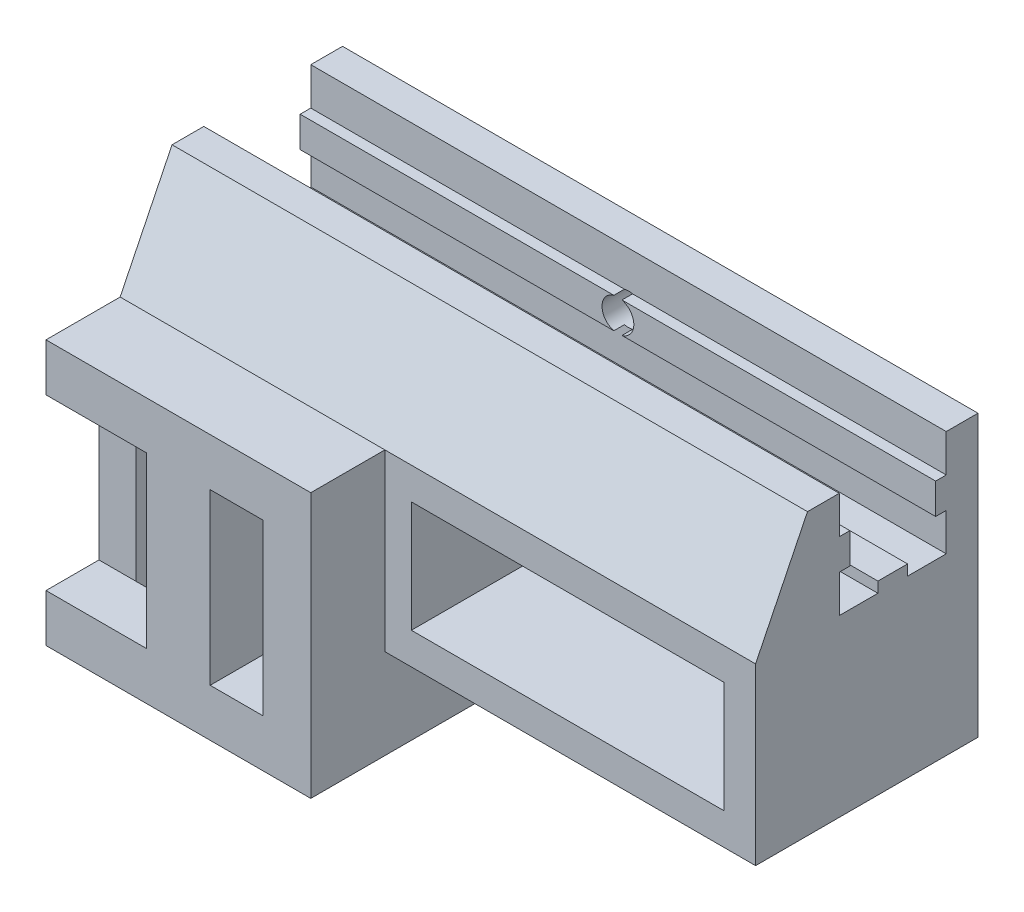
SolidWorks part; units mm, degrees
ref_plane "Front Plane" through (0, 0, 0) normal (0, 0, 1) x (1, 0, 0)
ref_plane "Top Plane" through (0, 0, 0) normal (0, 1, 0) x (1, 0, 0)
ref_plane "Right Plane" through (0, 0, 0) normal (1, 0, 0) x (0, 0, -1)
sketch "Esquisse1" plane through (0, 0, 0) normal (0, 0, 1) x (1, 0, 0)
  line L1 (-30, 17.5) -> (30, 17.5)
  line L2 (-30, 17.5) -> (-30, -17.5)
  line L3 (-30, -17.5) -> (30, -17.5)
  line L4 (30, 17.5) -> (30, -17.5)
  point P4 (-30, 0)
  point P6 (0, 17.5)
  dimension "D1" = 35
  dimension "D2" = 60
extrude "Main" add sketch "Esquisse1" along normal blind 3
sketch "Esquisse2" plane through (0, 0, 3) normal (0, 0, 1) x (1, 0, 0)
  line L0 (-30, 17.5) -> (-30, -17.5) construction
  line L1 (-30, 11.05) -> (30, 11.05)
  line L2 (-30, 11.05) -> (-30, 13.95)
  line L3 (-30, 13.95) -> (30, 13.95)
  line L4 (30, 11.05) -> (30, 13.95)
  line L5 (30, -17.5) -> (30, 17.5) construction
  line L6 (30, 17.5) -> (-30, 17.5) construction
  point P8 (-30, 12.5)
  dimension "D1" = 5
  dimension "D2" = 2.9
extrude "HorizontalMakerBeamRail1" add sketch "Esquisse2" along normal blind 1
sketch "Esquisse3" plane through (0, 0, 0) normal (0, 0, -1) x (-1, 0, 0)
  line L0 (-30, 11.05) -> (-30, 13.95) construction
  line L1 (-30, 17.5) -> (30, 17.5) construction
  circle A0 centre (0, 12.5) radius 1.5
  point P6 (-30, 12.5)
  point P9 (0, 17.5)
  dimension "D1" = 3
extrude "VerticalFixHole" cut sketch "Esquisse3" against normal through all
sketch "Esquisse4" plane through (0, 0, 3) normal (0, 0, 1) x (1, 0, 0)
  line L0 (-30, -17.5) -> (30, -17.5) construction
  line L1 (-30, -17.5) -> (-5, -17.5)
  line L2 (-30, -17.5) -> (-30, 7.5)
  line L3 (-30, 7.5) -> (-5, 7.5)
  line L4 (-5, -17.5) -> (-5, 7.5)
  line L5 (-30, 11.05) -> (-30, -17.5) construction
  line L6 (30, 17.5) -> (-30, 17.5) construction
  line L7 (-26.5, 4) -> (-8.5, 4)
  line L8 (-26.5, 4) -> (-26.5, -14)
  line L9 (-26.5, -14) -> (-8.5, -14)
  line L10 (-8.5, 4) -> (-8.5, -14)
  point P6 (-17.5, 4)
  point P13 (-17.5, 7.5)
  point P14 (-26.5, -5)
  point P15 (-30, -5)
  dimension "D1" = 10
  dimension "D2" = 18
  dimension "D3" = 3.5
extrude "UrgencyButton" add sketch "Esquisse4" along normal blind 20
sketch "Esquisse5" plane through (0, 0, 23) normal (0, 0, 1) x (1, 0, 0)
  line L1 (-26.5, 4) -> (-8.5, 4)
  line L2 (-26.5, 4) -> (-26.5, -14)
  line L3 (-26.5, -14) -> (-8.5, -14)
  line L4 (-8.5, 4) -> (-8.5, -14)
extrude "UrgencyButtonHole" cut sketch "Esquisse5" against normal through all and the other way through all
sketch "Esquisse6" plane through (0, 0, 23) normal (0, 0, 1) x (1, 0, 0)
  line L0 (-5, 7.5) -> (-30, 7.5) construction
  line L1 (-30, -17.5) -> (-5, -17.5)
  line L2 (-5, -17.5) -> (-5, 7.5)
  line L4 (-30, 7.5) -> (-30, 3)
  line L5 (-30, -17.5) -> (-5, -17.5) construction
  line L6 (-8.5, 4) -> (-26.5, 4) construction
  line L7 (-9.5, 3) -> (-30, 3)
  line L8 (-9.5, 3) -> (-9.5, -13)
  line L9 (-9.5, -13) -> (-30, -13)
  line L12 (-8.5, -14) -> (-8.5, 4) construction
  line L13 (-30, -13) -> (-30, -17.5)
  line L15 (-5, 7.5) -> (-30, 7.5)
  line L16 (-30, 7.5) -> (-30, -17.5) construction
  dimension "D2" = 1
  dimension "D3" = 1
extrude "Boss.-Extru.4" add sketch "Esquisse6" along normal blind 5
sketch "Esquisse7" plane through (0, 0, 28) normal (0, 0, 1) x (1, 0, 0)
  line L0 (-5, 7.5) -> (-30, 7.5) construction
  line L1 (-20.5, 7.5) -> (-14.5, 7.5)
  line L2 (-20.5, 7.5) -> (-20.5, -17.5)
  line L3 (-20.5, -17.5) -> (-14.5, -17.5)
  line L4 (-14.5, 7.5) -> (-14.5, -17.5)
  line L5 (-30, -17.5) -> (-5, -17.5) construction
  line L6 (-26.5, 3) -> (-26.5, -13) construction
  dimension "D1" = 6
  dimension "D2" = 6
extrude "Boss.-Extru.5" add sketch "Esquisse7" against normal up to surface (5 mm away) up to face at (-28.25, -5, 23)
sketch "Esquisse8" plane through (0, 0, 0) normal (0, 0, -1) x (-1, 0, 0)
  line L0 (5, -17.5) -> (5, 7.5) construction
  line L1 (2.5, -6) -> (-27, -6)
  line L2 (2.5, -6) -> (2.5, 4.5)
  line L3 (2.5, 4.5) -> (-27, 4.5)
  line L4 (-27, -6) -> (-27, 4.5)
  line L5 (-30, 17.5) -> (30, 17.5) construction
  dimension "D1" = 10.5
  dimension "D2" = 29.5
  dimension "D3" = 2.5
  dimension "D4" = 13
extrude "SwitchHole" cut sketch "Esquisse8" against normal through all
sketch "Esquisse10" plane through (0, 0, 3) normal (0, 0, 1) x (1, 0, 0)
  line L0 (-5, -17.5) -> (-5, 7.5) construction
  line L1 (-5, -9) -> (30, -9)
  line L2 (-5, -9) -> (-5, 7.5)
  line L3 (-5, 7.5) -> (30, 7.5)
  line L4 (30, -9) -> (30, 7.5)
  line L6 (-2.5, -6) -> (27, -6) construction
  line L7 (27, -6) -> (27, 4.5) construction
  line L8 (30, -17.5) -> (30, 11.05) construction
  line L9 (-2.5, -6) -> (27, -6)
  line L10 (-2.5, -6) -> (-2.5, 4.5)
  line L11 (-2.5, 4.5) -> (27, 4.5)
  line L12 (27, -6) -> (27, 4.5)
  line L13 (-5, 7.5) -> (-30, 7.5) construction
  dimension "D1" = 3
  dimension "D2" = 3
extrude "Boss.-Extru.6" add sketch "Esquisse10" along normal blind 18
sketch "Esquisse11" plane through (0, 0, 3) normal (0, 0, 1) x (1, 0, 0)
  line L1 (-5, -9) -> (30, -9)
  line L2 (-5, -9) -> (-5, -17.5)
  line L3 (-5, -17.5) -> (30, -17.5)
  line L4 (30, -9) -> (30, -17.5)
extrude "Enlèv. mat.-Extru.4" cut sketch "Esquisse11" against normal through all
sketch "Esquisse12" plane through (0, 7.5, 0) normal (0, 1, 0) x (1, 0, 0)
  line L0 (30, -21) -> (30, -3) construction
  line L1 (-30, -9.45) -> (30, -9.45)
  line L2 (-30, -9.45) -> (-30, -6.65)
  line L3 (-30, -6.65) -> (30, -6.65)
  line L4 (30, -9.45) -> (30, -6.65)
  line L5 (-30, -28) -> (-30, -3) construction
  point P9 (-30, -8.05)
  dimension "D1" = 2.8
  dimension "D2" = 5.05
extrude "Boss.-Extru.7" add sketch "Esquisse12" along normal blind 1
sketch "Esquisse13" plane through (30, 0, 0) normal (1, 0, 0) x (0, 0, -1)
  line L0 (-4, 13.95) -> (-3, 13.95) construction
  line L1 (-21, 7.5) -> (-9.45, 7.5) construction
  line L2 (-4, 11.05) -> (-3, 11.05) construction
  line L3 (-13.1, 7.5) -> (-13.1, 11.05)
  line L4 (-13.1, 11.05) -> (-12.1, 11.05)
  line L5 (-12.1, 11.05) -> (-12.1, 13.95)
  line L6 (-12.1, 13.95) -> (-13.1, 13.95)
  line L7 (-13.1, 13.95) -> (-13.1, 17.5)
  line L8 (-13.1, 17.5) -> (-16.1, 17.5)
  line L9 (-16.1, 17.5) -> (-16.1, 7.5)
  line L10 (-16.1, 7.5) -> (-13.1, 7.5)
  line L12 (-3, 7.5) -> (-3, 11.05) construction
  line L13 (-3, 17.5) -> (0, 17.5) construction
  point P5 (-12.6, 13.95)
  dimension "D1" = 10.1
extrude "Boss.-Extru.8" add sketch "Esquisse13" against normal through all
sketch "Esquisse14" plane through (30, 0, 0) normal (1, 0, 0) x (0, 0, -1)
  line L0 (-16.1, 7.5) -> (-16.1, 17.5)
  line L1 (-16.1, 17.5) -> (-16.1, 7.5) construction
  line L2 (-16.1, 17.5) -> (-21, 7.5)
  line L3 (-21, 7.5) -> (-16.1, 7.5)
extrude "Boss.-Extru.9" add sketch "Esquisse14" against normal through all
